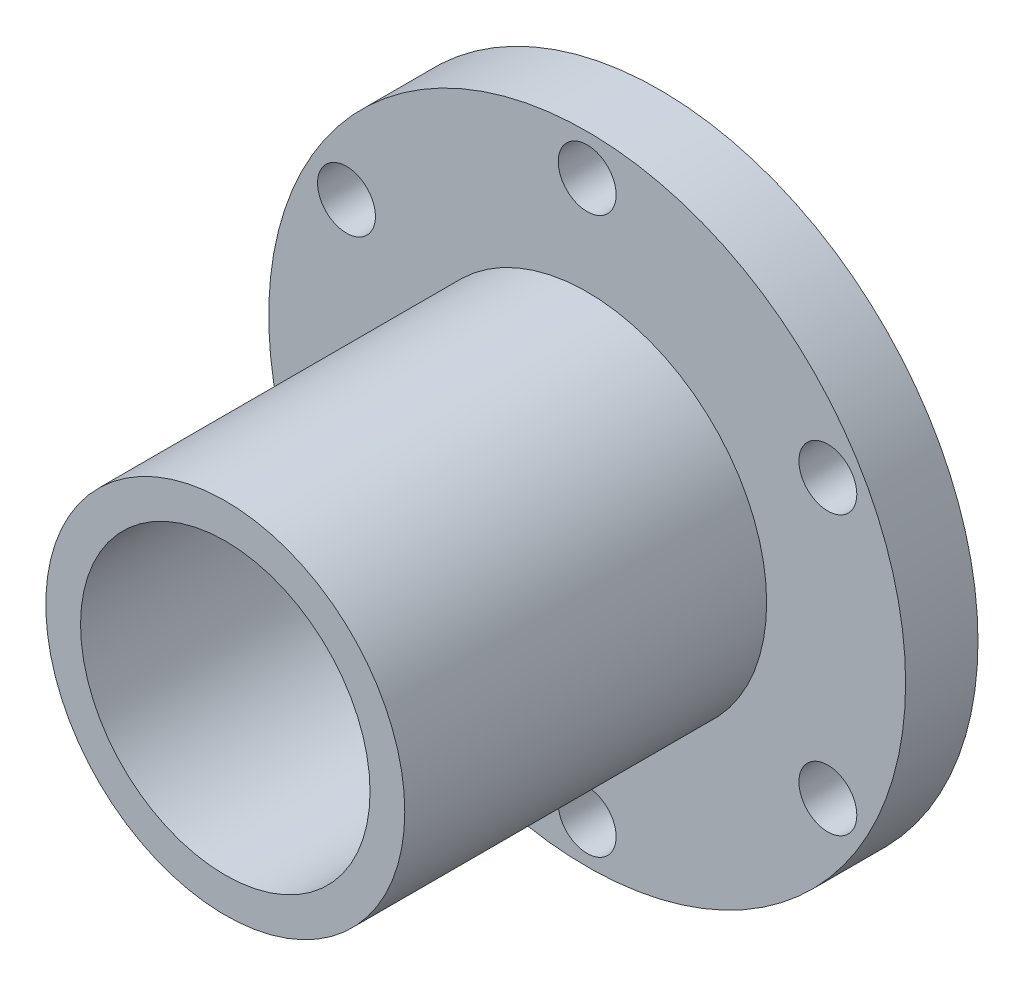
SolidWorks part; units mm, degrees
ref_plane "Front Plane" through (0, 0, 0) normal (0, 0, 1) x (1, 0, 0)
ref_plane "Top Plane" through (0, 0, 0) normal (0, 1, 0) x (1, 0, 0)
ref_plane "Right Plane" through (0, 0, 0) normal (1, 0, 0) x (0, 0, -1)
sketch "Sketch1" plane through (0, 0, 0) normal (0, 0, 1) x (1, 0, 0)
  line L0 (0, 0) -> (0, 44.125) construction
  line L1 (-83.1384, -48) -> (0, 0) construction
  circle A0 centre (0, 0) radius 110
  circle A2 centre (0, 0) radius 96 construction
  circle A3 centre (0, -96) radius 10
  circle A4 centre (-83.1384, -48) radius 10
  circle A5 centre (-83.1384, 48) radius 10
  circle A6 centre (0, 96) radius 10
  circle A7 centre (83.1384, 48) radius 10
  circle A8 centre (83.1384, -48) radius 10
  point P18 (0, 0)
  dimension "D1" = 220
  dimension "D2" = 192
  dimension "D3" = 20
  dimension "D5" = 120
  dimension "D4" = 6
extrude "Boss-Extrude1" add sketch "Sketch1" along normal blind 25
sketch "Sketch2" plane through (0, 0, 25) normal (0, 0, 1) x (1, 0, 0)
  circle A0 centre (0, 0) radius 62
  dimension "D1" = 124
extrude "Boss-Extrude2" add sketch "Sketch2" along normal blind 125
sketch "Sketch3" plane through (0, 0, 150) normal (0, 0, 1) x (1, 0, 0)
  circle A0 centre (0, 0) radius 50
  dimension "D1" = 100
extrude "Cut-Extrude1" cut sketch "Sketch3" against normal through all
